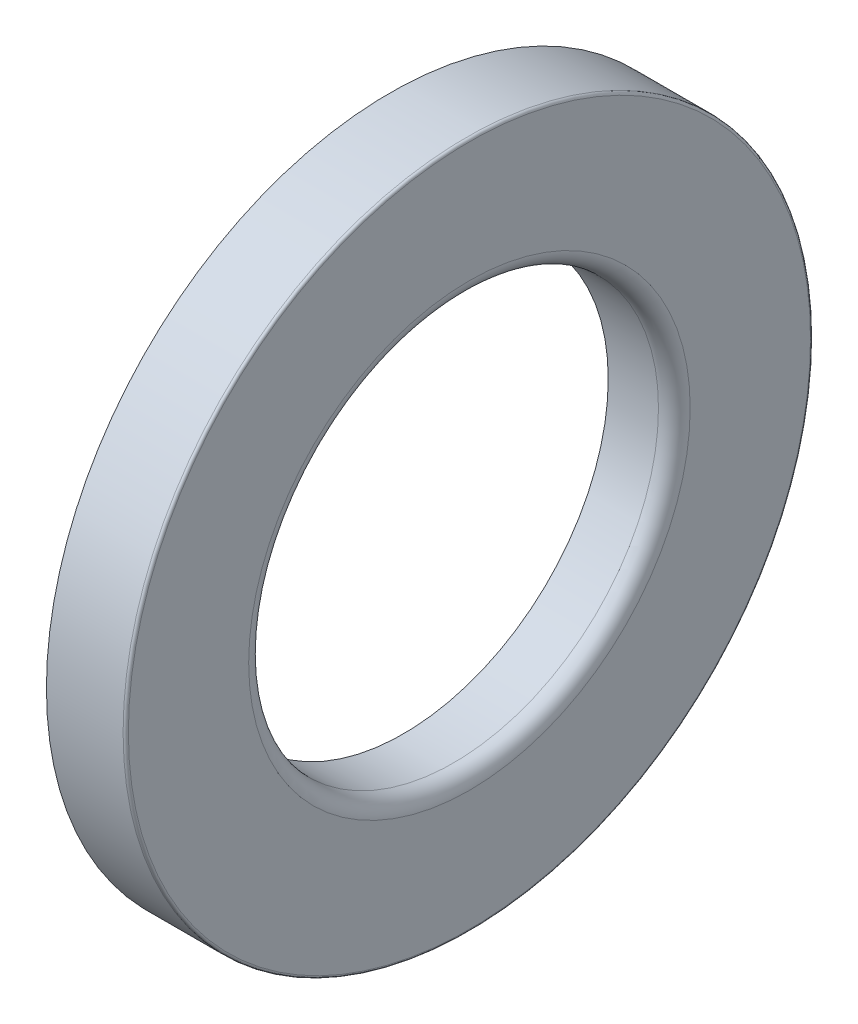
SolidWorks part; units mm, degrees
ref_plane "Plan de face" through (0, 0, 0) normal (0, 0, 1) x (1, 0, 0)
ref_plane "Plan de dessus" through (0, 0, 0) normal (0, 1, 0) x (1, 0, 0)
ref_plane "Plan de droite" through (0, 0, 0) normal (1, 0, 0) x (0, 0, -1)
sketch "Esquisse1" plane through (0, 0, 0) normal (0, 0, 1) x (1, 0, 0)
  line L0 (-5.9564, 0) -> (2.2454, 0) construction
  line L1 (0, 8.75) -> (0, 12)
  line L2 (-0.5, 12.5) -> (-2.5, 12.5)
  line L3 (-0.5, 8.25) -> (-2, 8.25)
  line L4 (-0.1, 7.75) -> (-2, 7.75)
  line L5 (0.5, 8.35) -> (0.5, 12.9)
  line L6 (0.4, 13) -> (-2.5, 13)
  line L7 (-2.5, 12.5) -> (-2.5, 13)
  line L8 (-2, 8.25) -> (-2, 7.75)
  line L9 (0, 8.25) -> (0, 12.5) construction
  line L10 (0, 12.5) -> (-2.5, 12.5) construction
  line L11 (0, 8.25) -> (-2, 8.25) construction
  line L12 (0.5, 7.75) -> (0.5, 13) construction
  line L13 (0.5, 13) -> (-2.5, 13) construction
  line L14 (0.5, 7.75) -> (-2, 7.75) construction
  arc A0 (0, 12) -> (-0.5, 12.5) centre (-0.5, 12) ccw
  arc A1 (-0.5, 8.25) -> (0, 8.75) centre (-0.5, 8.75) ccw
  arc A2 (0.5, 12.9) -> (0.4, 13) centre (0.4, 12.9) ccw
  arc A3 (-0.1, 7.75) -> (0.5, 8.35) centre (-0.1, 8.35) ccw
  point P20 (0.5, 13)
  dimension "D6" = 0.5
  dimension "D7" = 0.1
  dimension "D8" = 0.6
  dimension "D2" = 15.5
  dimension "D3" = 26
  dimension "D4" = 3
  dimension "D5" = 2.5
  dimension "D1" = 0.5
revolve "Révolution1" add sketch "Esquisse1" angle 360 about L0
